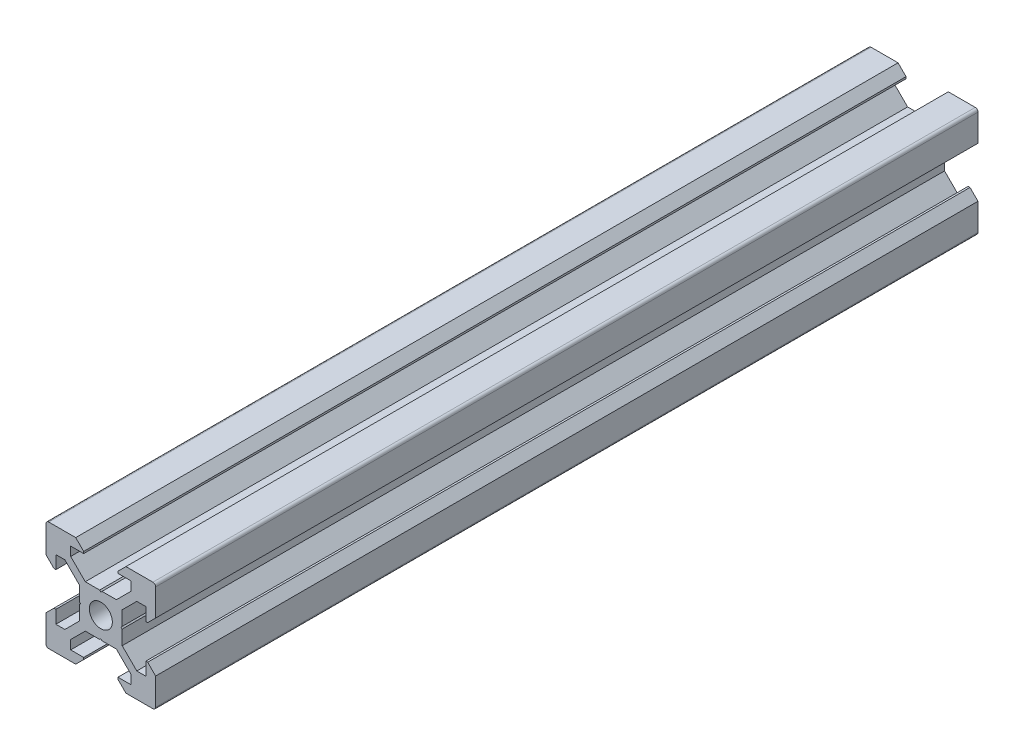
SolidWorks part; units mm, degrees
material "6061-T6 (SS)"
ref_plane "Front Plane" through (0, 0, 0) normal (0, 0, 1) x (1, 0, 0)
ref_plane "Top Plane" through (0, 0, 0) normal (0, 1, 0) x (1, 0, 0)
ref_plane "Right Plane" through (0, 0, 0) normal (1, 0, 0) x (0, 0, -1)
sketch "Sketch1" plane through (0, 0, 0) normal (0, 0, 1) x (1, 0, 0)
  line L1 (9.5, -10) -> (-9.5, -10)
  line L2 (10, -9.5) -> (10, 9.5)
  line L3 (9.5, 10) -> (-9.5, 10)
  line L4 (-10, -9.5) -> (-10, 9.5)
  line L5 (10, -10) -> (-10, 10) construction
  line L6 (10, 10) -> (-10, -10) construction
  circle A0 centre (0, 0) radius 2.1
  arc A1 (-9.5, 10) -> (-10, 9.5) centre (-9.5, 9.5) ccw
  arc A2 (10, 9.5) -> (9.5, 10) centre (9.5, 9.5) ccw
  arc A3 (9.5, -10) -> (10, -9.5) centre (9.5, -9.5) ccw
  arc A4 (-9.5, -10) -> (-10, -9.5) centre (-9.5, -9.5) cw
  point P0 (0, 0)
  line B0 (0, 0) -> (0, 10) construction
  line B1 (0, 3.69) -> (-0.21, 3.9)
  line B2 (-0.21, 3.9) -> (-2.8393, 3.9)
  line B3 (-2.8393, 3.9) -> (-5.5, 6.5607)
  line B4 (-5.5, 6.5607) -> (-5.5, 8.2)
  line B5 (-5.5, 8.2) -> (-3.125, 8.2)
  line B6 (-3.125, 8.2) -> (-3.125, 8.545)
  line B7 (-3.125, 8.545) -> (-4.58, 10)
  line B8 (-4.58, 10) -> (4.58, 10)
  line B9 (0, 0) -> (-5.9132, 5.9132) construction
  line B10 (3.125, 8.545) -> (4.58, 10)
  line B11 (3.125, 8.2) -> (3.125, 8.545)
  line B12 (5.5, 8.2) -> (3.125, 8.2)
  line B13 (5.5, 6.5607) -> (5.5, 8.2)
  line B14 (2.8393, 3.9) -> (5.5, 6.5607)
  line B15 (0.21, 3.9) -> (2.8393, 3.9)
  line B16 (0, 3.69) -> (0.21, 3.9)
  line B17 (0, 0) -> (-10, 0) construction
  line B18 (-3.69, 0) -> (-3.9, -0.21)
  line B19 (-3.9, -0.21) -> (-3.9, -2.8393)
  line B20 (-3.9, -2.8393) -> (-6.5607, -5.5)
  line B21 (-6.5607, -5.5) -> (-8.2, -5.5)
  line B22 (-8.2, -5.5) -> (-8.2, -3.125)
  line B23 (-8.2, -3.125) -> (-8.545, -3.125)
  line B24 (-8.545, -3.125) -> (-10, -4.58)
  line B25 (-10, -4.58) -> (-10, 4.58)
  line B26 (0, 0) -> (-5.9132, -5.9132) construction
  line B27 (-8.545, 3.125) -> (-10, 4.58)
  line B28 (-8.2, 3.125) -> (-8.545, 3.125)
  line B29 (-8.2, 5.5) -> (-8.2, 3.125)
  line B30 (-6.5607, 5.5) -> (-8.2, 5.5)
  line B31 (-3.9, 2.8393) -> (-6.5607, 5.5)
  line B32 (-3.9, 0.21) -> (-3.9, 2.8393)
  line B33 (-3.69, 0) -> (-3.9, 0.21)
  line B34 (0, 0) -> (0, -10) construction
  line B35 (0, -3.69) -> (0.21, -3.9)
  line B36 (0.21, -3.9) -> (2.8393, -3.9)
  line B37 (2.8393, -3.9) -> (5.5, -6.5607)
  line B38 (5.5, -6.5607) -> (5.5, -8.2)
  line B39 (5.5, -8.2) -> (3.125, -8.2)
  line B40 (3.125, -8.2) -> (3.125, -8.545)
  line B41 (3.125, -8.545) -> (4.58, -10)
  line B42 (4.58, -10) -> (-4.58, -10)
  line B43 (0, 0) -> (5.9132, -5.9132) construction
  line B44 (-3.125, -8.545) -> (-4.58, -10)
  line B45 (-3.125, -8.2) -> (-3.125, -8.545)
  line B46 (-5.5, -8.2) -> (-3.125, -8.2)
  line B47 (-5.5, -6.5607) -> (-5.5, -8.2)
  line B48 (-2.8393, -3.9) -> (-5.5, -6.5607)
  line B49 (-0.21, -3.9) -> (-2.8393, -3.9)
  line B50 (0, -3.69) -> (-0.21, -3.9)
  line B51 (0, 0) -> (10, 0) construction
  line B52 (3.69, 0) -> (3.9, 0.21)
  line B53 (3.9, 0.21) -> (3.9, 2.8393)
  line B54 (3.9, 2.8393) -> (6.5607, 5.5)
  line B55 (6.5607, 5.5) -> (8.2, 5.5)
  line B56 (8.2, 5.5) -> (8.2, 3.125)
  line B57 (8.2, 3.125) -> (8.545, 3.125)
  line B58 (8.545, 3.125) -> (10, 4.58)
  line B59 (10, 4.58) -> (10, -4.58)
  line B60 (0, 0) -> (5.9132, 5.9132) construction
  line B61 (8.545, -3.125) -> (10, -4.58)
  line B62 (8.2, -3.125) -> (8.545, -3.125)
  line B63 (8.2, -5.5) -> (8.2, -3.125)
  line B64 (6.5607, -5.5) -> (8.2, -5.5)
  line B65 (3.9, -2.8393) -> (6.5607, -5.5)
  line B66 (3.9, -0.21) -> (3.9, -2.8393)
  line B67 (3.69, 0) -> (3.9, -0.21)
  dimension "D1" = 4.2
  dimension "D3" = 0.5
  dimension "D2" = 20
sketch_block_instance "V Slot 1-4"
sketch_block "V Slot 1" parameters "D1"=10, "D2"=11, "D3"=4.3, "D4"=1.8, "D5"=0.21, "D6"=45, "D7"=9.16, "D8"=1.5, "D9"=6.25
sketch_block_instance "V Slot 1-5"
sketch_block_instance "V Slot 1-6"
sketch_block_instance "V Slot 1-7"
extrude "Boss-Extrude1" add sketch "Sketch1" along normal blind 150 contours B67 B52 B53 B54 B55 B56 B57 B58 L2 A2 L3 B10 B11 B12 B13 B14 B15 B16 B1 B2 B3 B4 B5 B6 B7 A1 L4 B27 B28 B29 B30 B31 B32 B33 B18 B19 B20 B21 B22 B23 B24 A4 L1 B44 B45 B46 B47 B48 B49
